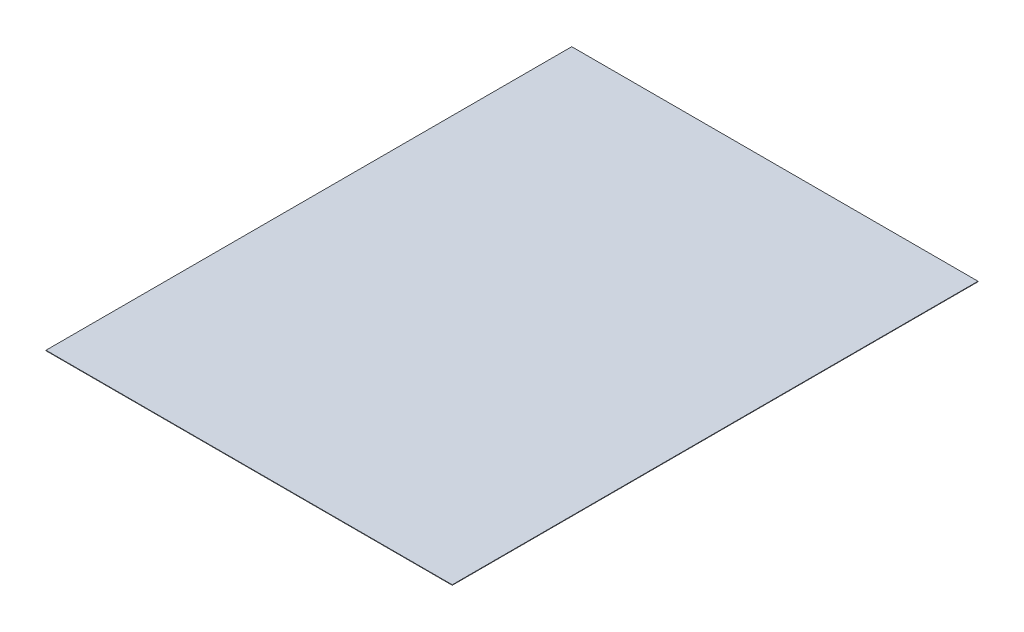
SolidWorks part; units mm, degrees
material "ABS"
ref_plane "Front Plane" through (0, 0, 0) normal (0, 0, 1) x (1, 0, 0)
ref_plane "Top Plane" through (0, 0, 0) normal (0, 1, 0) x (1, 0, 0)
ref_plane "Right Plane" through (0, 0, 0) normal (1, 0, 0) x (0, 0, -1)
sketch "Sketch1" plane through (0, 0, 0) normal (0, 1, 0) x (1, 0, 0)
  line L1 (0, 0) -> (215.9, 0)
  line L2 (0, 0) -> (0, 279.4)
  line L3 (0, 279.4) -> (215.9, 279.4)
  line L4 (215.9, 0) -> (215.9, 279.4)
  dimension "D1" = 279.4
  dimension "D2" = 215.9
extrude "Boss-Extrude1" add sketch "Sketch1" along normal blind 0.254
sketch "Sketch2" plane through (0, 0.254, 0) normal (0, 1, 0) x (1, 0, 0)
  line L0 (0, 279.4) -> (215.9, 0) construction
  line L1 (215.9, 279.4) -> (0, 0) construction
sketch "Sketch3" plane through (0, 0.254, 0) normal (0, 1, 0) x (1, 0, 0)
  line L0 (0, 279.4) -> (215.9, 0) construction
  point P0 (107.95, 139.7)
